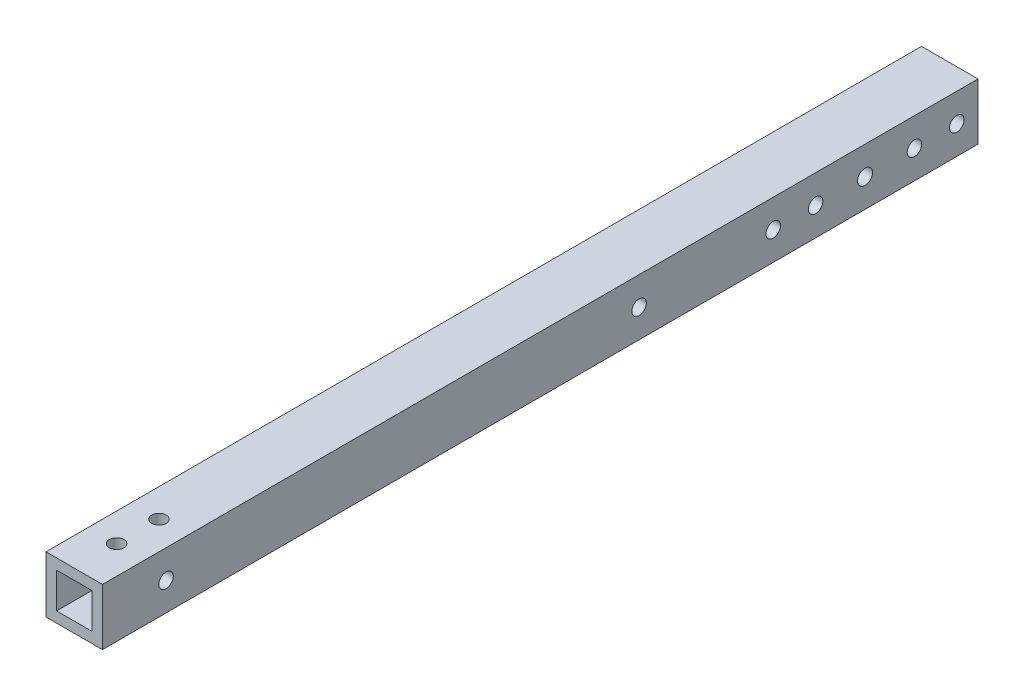
SolidWorks part; units mm, degrees
material "6061-T6 (SS)"
ref_plane "Front Plane" through (0, 0, 0) normal (0, 0, 1) x (1, 0, 0)
ref_plane "Top Plane" through (0, 0, 0) normal (0, 1, 0) x (1, 0, 0)
ref_plane "Right Plane" through (0, 0, 0) normal (1, 0, 0) x (0, 0, -1)
sketch "Sketch2" plane through (0, 0, 0) normal (0, 0, 1) x (1, 0, 0)
  line L0 (0, 12.7) -> (0, -12.7) construction
  line L1 (-12.7, 0) -> (12.7, 0) construction
  line L2 (3.2512, -12.7) -> (12.7, -12.7)
  line L3 (12.7, -12.7) -> (12.7, -3.2512)
  line L4 (3.2512, -12.7) -> (3.2512, -10.4902)
  line L5 (3.2512, -10.4902) -> (8.9276, -10.4902)
  line L6 (8.9276, -10.4902) -> (3.0856, -4.6482)
  line L7 (0, 0) -> (12.7, -12.7) construction
  line L8 (12.7, -3.2512) -> (10.4902, -3.2512)
  line L9 (10.4902, -3.2512) -> (10.4902, -8.9276)
  line L10 (10.4902, -8.9276) -> (4.6482, -3.0856)
  circle A0 centre (0, 0) radius 2.6035
  arc A1 (6.3485, -10.4902) -> (7.1039, -8.6665) centre (6.3485, -9.4219) ccw construction
  point P8 (0, -4.6482)
  dimension "Center Hole Diameter" = 5.207
  dimension "Rail Height" = 25.4
  dimension "Rail Width" = 25.4
  dimension "T-Slot Width" = 6.5024
  dimension "Slot Inner Width" = 14.8336
  dimension "Thickness" = 2.2098
  dimension "Slot Depth" = 5.842
  dimension "D1" = 2.2098
sketch "Sketch3" plane through (0, 0, 0) normal (1, 0, 0) x (0, 0, -1)
  line L0 (-196.85, -12.7) -> (196.85, -12.7) construction
  line L1 (-171.45, 0) -> (171.45, 0) construction
  dimension "Length" = 393.7
  dimension "D1" = 25.4
sketch "Sketch4" plane through (0, 0, 0) normal (0, 0, 1) x (1, 0, 0)
  line L2 (-7.9375, 7.9375) -> (7.9375, 7.9375)
  line L3 (-7.9375, 7.9375) -> (-7.9375, -7.9375)
  line L7 (-7.9375, -7.9375) -> (7.9375, -7.9375)
  line L9 (7.9375, 7.9375) -> (7.9375, -7.9375)
  line L10 (-7.9375, 7.9375) -> (7.9375, -7.9375) construction
  line L11 (-7.9375, -7.9375) -> (7.9375, 7.9375) construction
  line L23 (-12.7, -12.7) -> (12.7, -12.7)
  line L24 (-12.7, -12.7) -> (-12.7, 12.7)
  line L25 (-12.7, 12.7) -> (12.7, 12.7)
  line L26 (12.7, -12.7) -> (12.7, 12.7)
  line L27 (-12.7, -12.7) -> (12.7, 12.7) construction
  line L28 (-12.7, 12.7) -> (12.7, -12.7) construction
  point P0 (0, 0)
  point P5 (0, 0)
  dimension "D1" = 25.4
  dimension "D2" = 15.875
extrude "Boss-Extrude1" add sketch "Sketch4" along normal mid plane 393.7
hole_wizard "F (0.257) Diameter Hole1" positions "Sketch5" profile "Sketch6" hole size "F" standard "ANSI Inch" end condition through all
sketch "Sketch5" plane through (-12.7, 0, 0) normal (-1, 0, 0) x (0, 0, 1)
  line L1 (-196.85, 12.7) -> (-196.85, -12.7) construction
  point P0 (-104.775, 0)
  point P2 (-123.825, 0)
  point P4 (-168.275, 0)
  point P6 (-187.325, 0)
  dimension "D1" = 19.05
  dimension "D2" = 19.05
  dimension "D3" = 44.45
  dimension "D4" = 9.525
sketch "Sketch6" plane through (-12.7, 0, -104.775) normal (0, 1, 0) x (0, 0, 1)
  line L0 (0, 0) -> (0, 25.4)
  line L1 (0, 25.4) -> (3.2639, 25.4)
  line L2 (3.2639, 25.4) -> (3.2639, 0)
  line L5 (3.2639, 0) -> (0, 0)
  line L11 (0, -6.35) -> (0, 107.95) construction
  dimension "Thru Hole Dia." = 6.5278
  dimension "Thru Hole Depth" = 25.4
hole_wizard "F (0.257) Diameter Hole2" positions "Sketch8" profile "Sketch9" hole size "F" standard "ANSI Inch" end condition through all
sketch "Sketch8" plane through (0, 12.7, 0) normal (0, 1, 0) x (1, 0, 0)
  line L0 (12.7, -196.85) -> (-12.7, -196.85) construction
  point P0 (0, -177.8)
  point P2 (0, -158.75)
  dimension "D1" = 19.05
  dimension "D2" = 19.05
sketch "Sketch9" plane through (0, 12.7, 177.8) normal (1, 0, 0) x (0, 0, 1)
  line L0 (0, 0) -> (0, 25.4)
  line L1 (0, 25.4) -> (3.2639, 25.4)
  line L2 (3.2639, 25.4) -> (3.2639, 0)
  line L5 (3.2639, 0) -> (0, 0)
  line L11 (0, -6.35) -> (0, 107.95) construction
  dimension "Thru Hole Dia." = 6.5278
  dimension "Thru Hole Depth" = 25.4
hole_wizard "F (0.257) Diameter Hole3" positions "Sketch10" profile "Sketch11" hole size "F" standard "ANSI Inch" end condition through all
sketch "Sketch10" plane through (-12.7, 0, 0) normal (-1, 0, 0) x (0, 0, 1)
  line L0 (196.85, 12.7) -> (196.85, -12.7) construction
  point P0 (168.275, 0)
  point P5 (-44.45, 0)
  dimension "D1" = 28.575
  dimension "D2" = 241.3
sketch "Sketch11" plane through (-12.7, 0, 168.275) normal (0, 1, 0) x (0, 0, 1)
  line L0 (0, 0) -> (0, 25.4)
  line L1 (0, 25.4) -> (3.2639, 25.4)
  line L2 (3.2639, 25.4) -> (3.2639, 0)
  line L5 (3.2639, 0) -> (0, 0)
  line L11 (0, -6.35) -> (0, 107.95) construction
  dimension "Thru Hole Dia." = 6.5278
  dimension "Thru Hole Depth" = 25.4
hole_wizard "17/64 (0.26563) Diameter Hole1" positions "Sketch13" profile "Sketch14" hole size "17/64" standard "ANSI Inch" end condition through all
sketch "Sketch13" plane through (-12.7, 0, 0) normal (-1, 0, 0) x (0, 0, 1)
  line L0 (-146.05, 0) -> (-168.275, 0) construction
  line L2 (-146.05, 0) -> (-123.825, 0) construction
  point P0 (-146.05, 0)
sketch "Sketch14" plane through (-12.7, 0, -146.05) normal (0, 1, 0) x (0, 0, 1)
  line L0 (0, 0) -> (0, 25.4)
  line L1 (0, 25.4) -> (3.3735, 25.4)
  line L2 (3.3735, 25.4) -> (3.3735, 0)
  line L5 (3.3735, 0) -> (0, 0)
  line L11 (0, -6.35) -> (0, 107.95) construction
  dimension "Thru Hole Dia." = 6.747
  dimension "Thru Hole Depth" = 25.4
equation "\"D1@Boss-Extrude1\"=\"Length@Sketch3\""
equation "\"D1@Sketch2\"=\"Thickness@Sketch2\""
equation "\"TinesBase\"=28"
equation "\"TinesBaseOML\"=15.5"
equation "\"Length@Sketch3\"= \"TinesBaseOML\""
